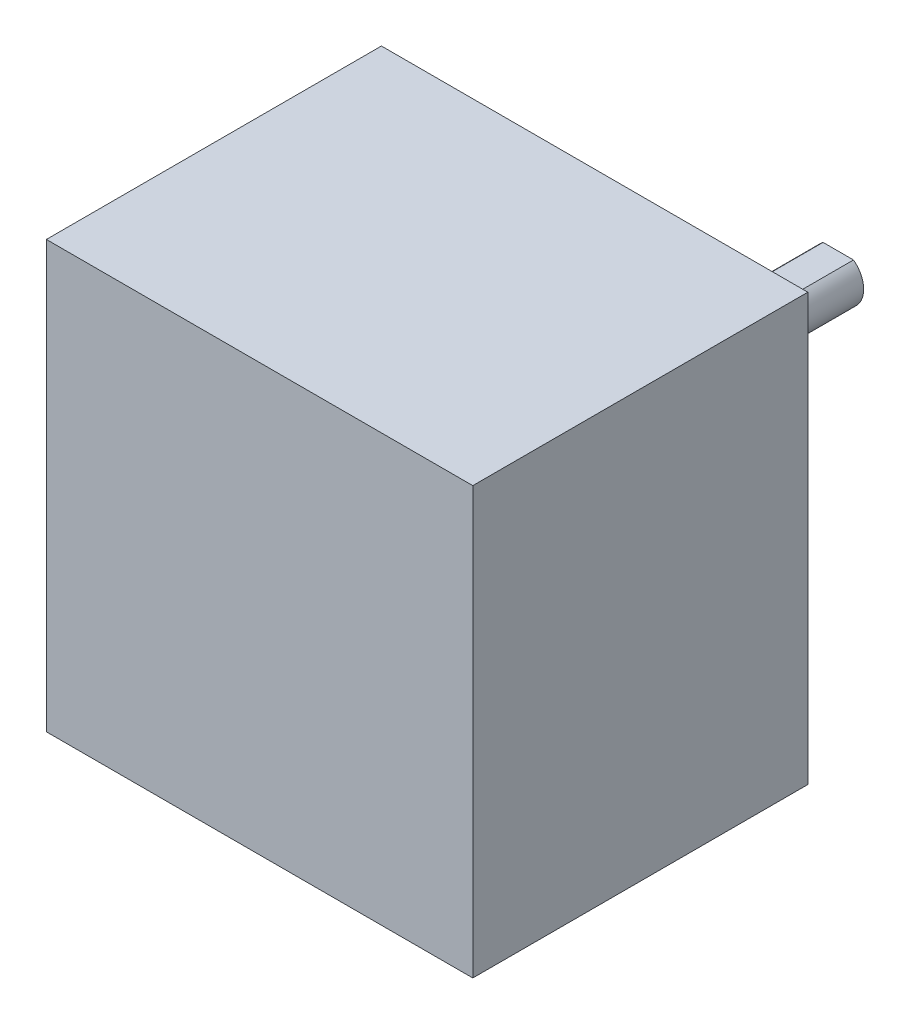
SolidWorks part; units mm, degrees
ref_plane "Front Plane" through (0, 0, 0) normal (0, 0, 1) x (1, 0, 0)
ref_plane "Top Plane" through (0, 0, 0) normal (0, 1, 0) x (1, 0, 0)
ref_plane "Right Plane" through (0, 0, 0) normal (1, 0, 0) x (0, 0, -1)
sketch "Sketch1" plane through (0, 0, 0) normal (0, 0, 1) x (1, 0, 0)
  line L1 (-21, -21) -> (21, -21)
  line L2 (-21, -21) -> (-21, 21)
  line L3 (-21, 21) -> (21, 21)
  line L4 (21, -21) -> (21, 21)
  line L5 (-21, -21) -> (21, 21) construction
  line L6 (-21, 21) -> (21, -21) construction
  point P0 (0, 0)
  dimension "D1" = 42
  dimension "D2" = 42
extrude "Boss-Extrude1" add sketch "Sketch1" along normal blind 33
sketch "Sketch2" plane through (0, 0, 0) normal (0, 0, -1) x (-1, 0, 0)
  circle A0 centre (0, 0) radius 11.7935
extrude "Boss-Extrude2" add sketch "Sketch2" along normal blind 2
sketch "Sketch3" plane through (0, 0, -2) normal (0, 0, -1) x (-1, 0, 0)
  circle A0 centre (0, 0) radius 2.5
  dimension "D1" = 5
extrude "Boss-Extrude3" add sketch "Sketch3" along normal blind 22
sketch "Sketch4" plane through (0, 0, -24) normal (0, 0, -1) x (-1, 0, 0)
  line L0 (0, 0) -> (0, 2) construction
  line L1 (1.5, 2) -> (-1.5, 2)
  circle A0 centre (0, 0) radius 2.5 construction
  arc A1 (-1.5, 2) -> (1.5, 2) centre (0, 0) cw
  point P8 (0, 2)
  circle M2 centre (0, 0) radius 2.5
  dimension "D1" = 2
extrude "Cut-Extrude1" cut sketch "Sketch4" against normal blind 20 contours L1 M2
